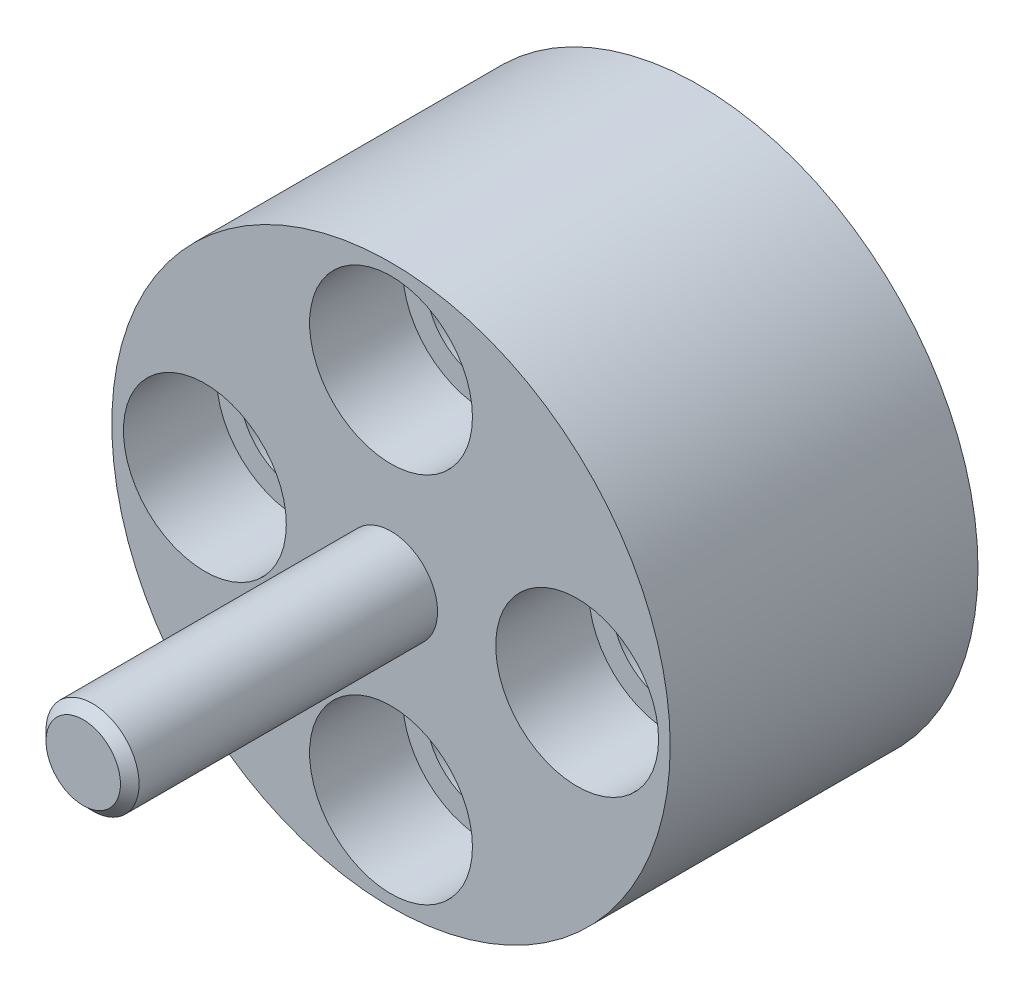
SolidWorks part; units mm, degrees
ref_plane "Front Plane" through (0, 0, 0) normal (0, 0, 1) x (1, 0, 0)
ref_plane "Top Plane" through (0, 0, 0) normal (0, 1, 0) x (1, 0, 0)
ref_plane "Right Plane" through (0, 0, 0) normal (1, 0, 0) x (0, 0, -1)
sketch "Sketch1" plane through (0, 0, 0) normal (0, 0, 1) x (1, 0, 0)
  line L0 (0, 12.7) -> (0, 0) construction
  line L1 (0, 0) -> (12.7, 0) construction
  line L2 (-12.7, 0) -> (0, 0) construction
  line L3 (0, -12.7) -> (0, 0) construction
  circle A0 centre (0, 0) radius 19.05
  circle A1 centre (0, 0) radius 5
  circle A2 centre (0, 12.7) radius 3.9688
  circle A3 centre (12.7, 0) radius 3.9688
  circle A4 centre (0, -12.7) radius 3.9688
  circle A5 centre (-12.7, 0) radius 3.9688
  dimension "D1" = 10
  dimension "D2" = 7.9375
  dimension "D4" = 38.1
  dimension "D3" = 12.7
extrude "Boss-Extrude1" add sketch "Sketch1" along normal blind 21
ref_plane "Plane1" through (0, 0, 6.858) normal (0, 0, -1) x (-1, 0, 0)
sketch "Sketch3" plane through (0, 0, 6.858) normal (0, 0, -1) x (-1, 0, 0)
  circle A0 centre (0, 0) radius 5
  circle A1 centre (0, 0) radius 5 construction
extrude "Boss-Extrude2" add sketch "Sketch3" along normal up to surface (14.142 mm away)
sketch "Sketch4" plane through (0, 0, 21) normal (0, 0, 1) x (1, 0, 0)
  circle A0 centre (0, 0) radius 3.175
  dimension "D1" = 6.35
extrude "Boss-Extrude3" add sketch "Sketch4" along normal blind 21
chamfer "Chamfer1" distance 0.635 angle 45 1 edges at (3.175, 0, 42)
hole_wizard "CBORE for 1/4 Socket Head Cap Screw1" positions "Sketch6" profile "Sketch5" counterbore size "1/4" standard "ANSI Inch" end condition through all
sketch "Sketch6" plane through (0, 0, 21) normal (0, 0, 1) x (1, 0, 0)
  point P0 (0, 12.7)
  point P3 (12.7, 0)
  point P6 (0, -12.7)
  point P9 (-12.7, 0)
sketch "Sketch5" plane through (0, 12.7, 21) normal (1, 0, 0) x (0, -1, 0)
  line L0 (0, 0) -> (0, 21)
  line L1 (0, 21) -> (3.3782, 21)
  line L3 (3.3782, 21) -> (3.3782, 6.35)
  line L4 (3.3782, 6.35) -> (5.5562, 6.35)
  line L5 (5.5562, 6.35) -> (5.5562, 0)
  line L7 (5.5562, 0) -> (0, 0)
  line L11 (0, -6.35) -> (0, 107.95) construction
  dimension "Thru Hole Dia." = 6.7564
  dimension "Thru Hole Depth" = 21
  dimension "C'Bore Dia." = 11.1125
  dimension "C'Bore Depth" = 6.35
hole_wizard "CBORE for 1/4 Socket Head Cap Screw2" positions "Sketch8" profile "Sketch7" counterbore size "1/4" standard "ANSI Inch"
sketch "Sketch8" plane through (0, 0, 0) normal (0, 0, -1) x (-1, 0, 0)
  point P0 (0, 0)
sketch "Sketch7" plane through (0, 0, 0) normal (1, 0, 0) x (0, 1, 0)
  line L0 (0, 0) -> (0, 2.0552)
  line L1 (0, 2.0552) -> (3.3782, 0.0254)
  line L2 (3.3782, 0.0254) -> (3.3782, 6.858)
  line L3 (3.3782, 6.858) -> (5.5562, 6.858)
  line L4 (5.5562, 6.858) -> (5.5562, 0)
  line L5 (5.5562, 0) -> (0, 0)
  line L10 (0, 2.0552) -> (-3.3782, 0.0254) construction
  line L11 (0, -6.35) -> (0, 107.95) construction
  dimension "Hole Dia." = 6.7564
  dimension "Hole Depth" = 0.0254
  dimension "C'Bore Dia." = 11.1125
  dimension "C'Bore Depth" = 6.858
  dimension "Drill Angle" = 118
